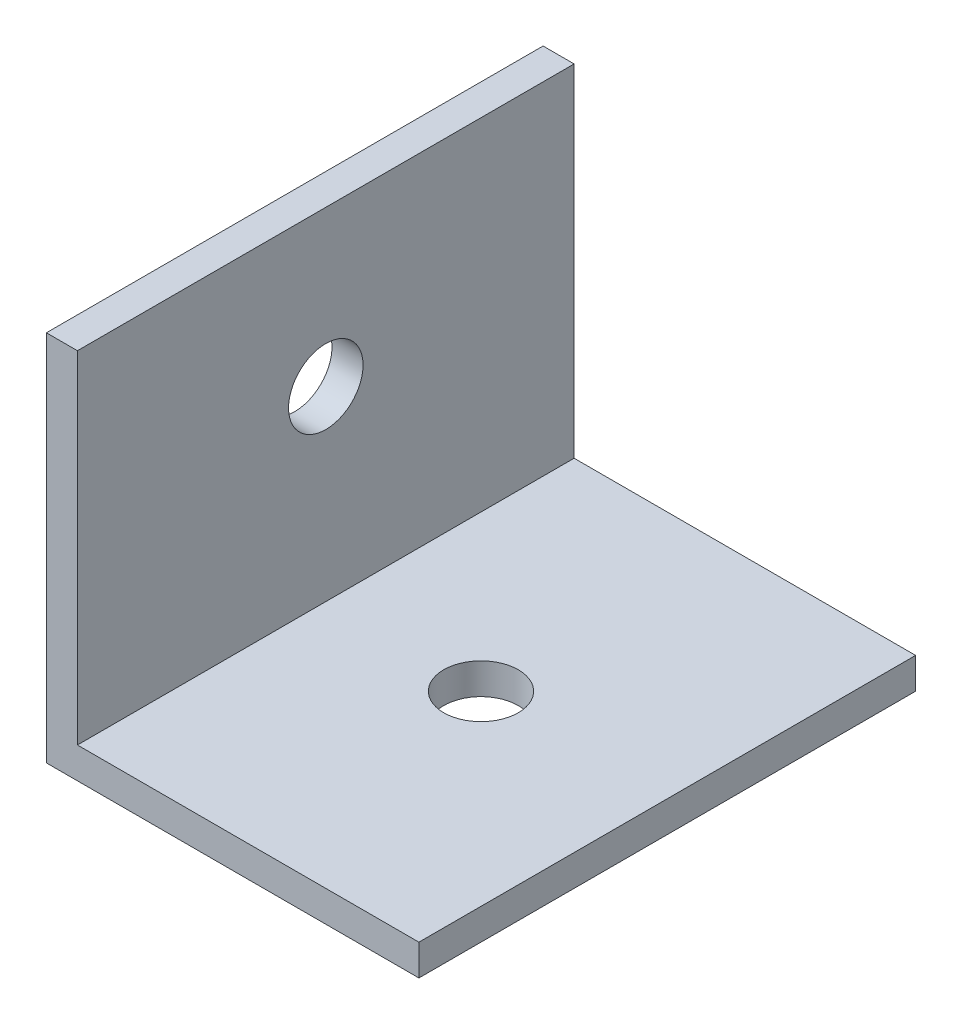
SolidWorks part; units mm, degrees
ref_plane "Front Plane" through (0, 0, 0) normal (0, 0, 1) x (1, 0, 0)
ref_plane "Top Plane" through (0, 0, 0) normal (0, 1, 0) x (1, 0, 0)
ref_plane "Right Plane" through (0, 0, 0) normal (1, 0, 0) x (0, 0, -1)
sketch "Sketch1" plane through (0, 0, 0) normal (0, 0, 1) x (1, 0, 0)
  line L0 (0, 0) -> (0, 60)
  line L1 (0, 0) -> (60, 0)
  dimension "D1" = 60
  dimension "D2" = 60
extrude "Extrude-Thin1" add sketch "Sketch1" along normal mid plane 80 thin
sketch "Sketch2" plane through (0, 0, 0) normal (0, -1, 0) x (1, 0, 0)
  line L0 (0, 40) -> (0, -40) construction
  circle A0 centre (30, 0) radius 6
  point P4 (0, 0)
  dimension "D1" = 12
  dimension "D2" = 30
extrude "Cut-Extrude1" cut sketch "Sketch2" against normal through all
sketch "Sketch3" plane through (0, 0, 0) normal (-1, 0, 0) x (0, -1, 0)
  line L1 (0, 40) -> (0, -40) construction
  circle A0 centre (-35, 0) radius 6
  point P4 (0, 0)
  dimension "D1" = 12
  dimension "D2" = 35
extrude "Cut-Extrude2" cut sketch "Sketch3" against normal through all
